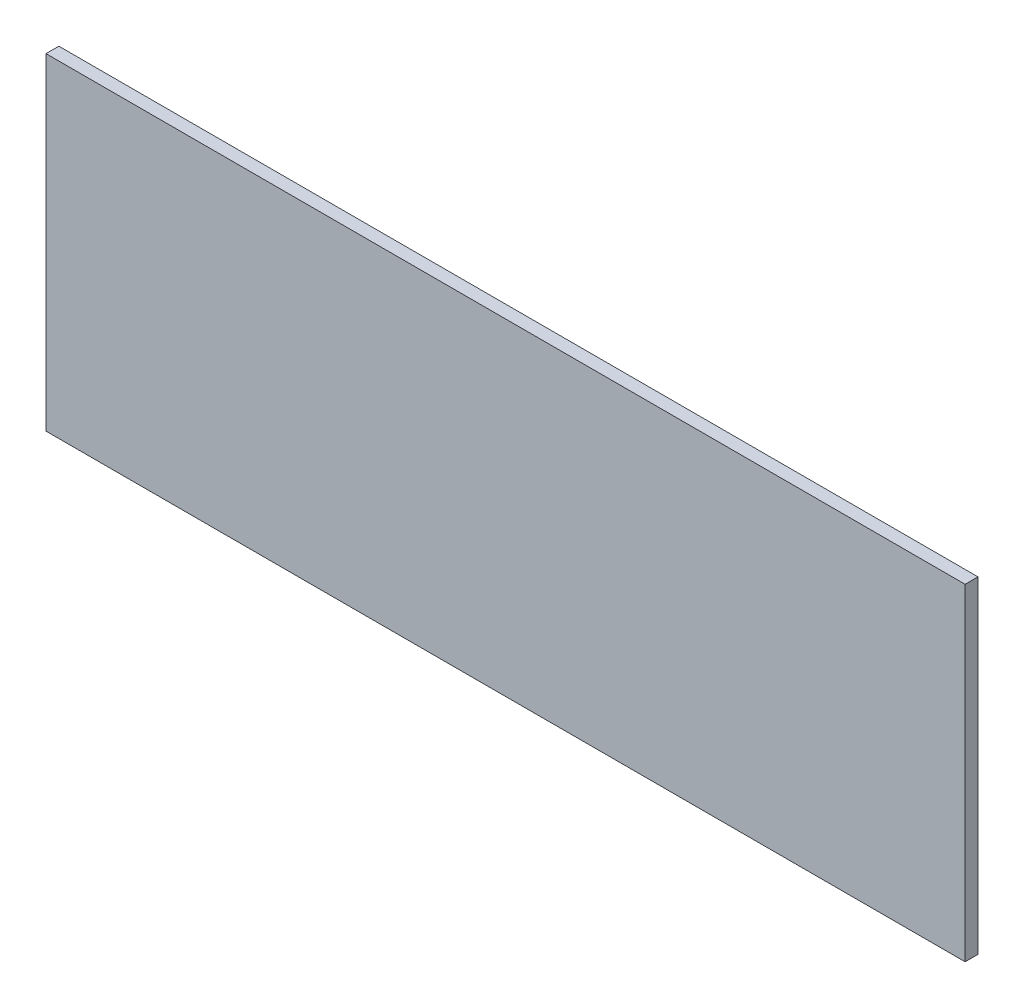
SolidWorks part; units mm, degrees
material "Acrylic (Medium-high impact)"
ref_plane "Front Plane" through (0, 0, 0) normal (0, 0, 1) x (1, 0, 0)
ref_plane "Top Plane" through (0, 0, 0) normal (0, 1, 0) x (1, 0, 0)
ref_plane "Right Plane" through (0, 0, 0) normal (1, 0, 0) x (0, 0, -1)
sketch "Sketch1" plane through (0, 0, 0) normal (0, 0, 1) x (1, 0, 0)
  line L1 (0, 0) -> (214.216, 0)
  line L2 (0, 0) -> (0, 76.2)
  line L3 (0, 76.2) -> (214.216, 76.2)
  line L4 (214.216, 0) -> (214.216, 76.2)
  dimension "D1" = 214.216
  dimension "D2" = 76.2
extrude "Boss-Extrude1" add sketch "Sketch1" along normal mid plane 3
sketch "Sketch2" plane through (0, 0, 1.5) normal (0, 0, 1) x (1, 0, 0)
  line L0 (0, 76.2) -> (214.216, 0) construction
  line L1 (214.216, 76.2) -> (0, 0) construction
  line L3 (30.908, 139.7) -> (183.308, 139.7)
  line L4 (30.908, 139.7) -> (30.908, -63.5)
  line L5 (30.908, -63.5) -> (183.308, -63.5)
  line L6 (183.308, 139.7) -> (183.308, -63.5)
  line L7 (30.908, 139.7) -> (183.308, -63.5) construction
  line L8 (30.908, -63.5) -> (183.308, 139.7) construction
  point P8 (107.108, 38.1)
  dimension "D1" = 152.4
  dimension "D2" = 203.2
